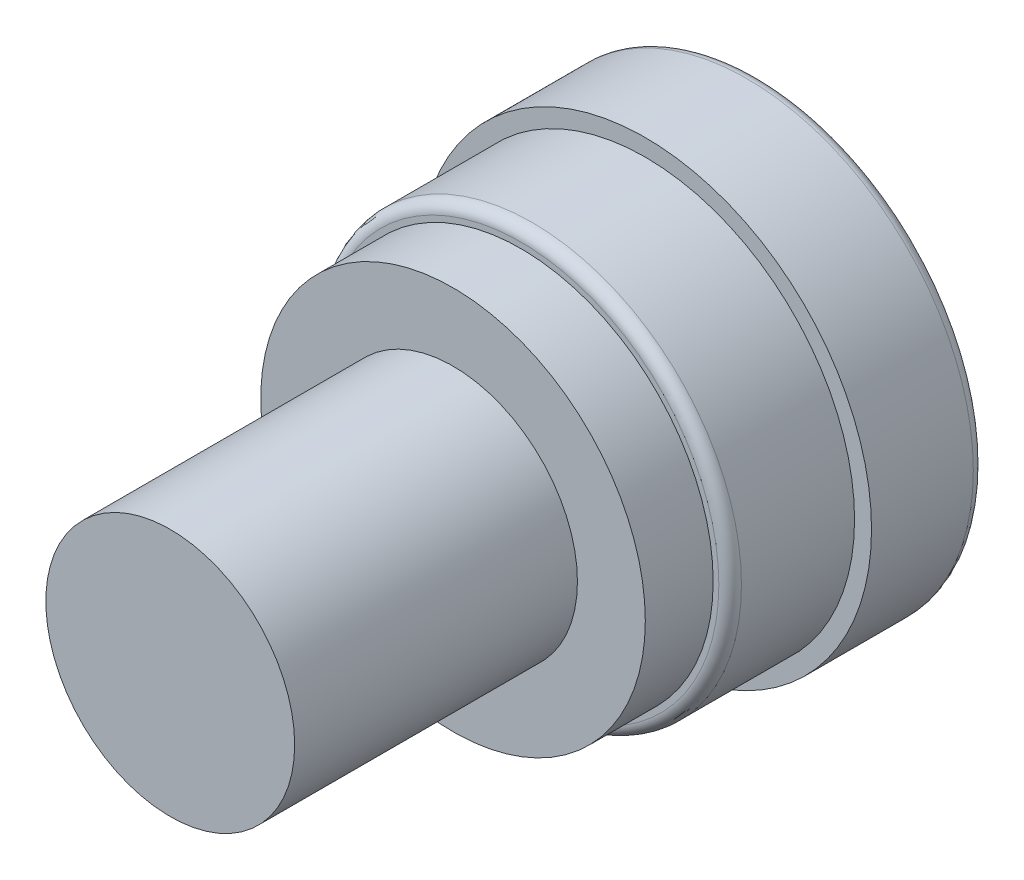
SolidWorks part; units mm, degrees
ref_plane "Front Plane" through (0, 0, 0) normal (0, 0, 1) x (1, 0, 0)
ref_plane "Top Plane" through (0, 0, 0) normal (0, 1, 0) x (1, 0, 0)
ref_plane "Right Plane" through (0, 0, 0) normal (1, 0, 0) x (0, 0, -1)
sketch "Sketch1" plane through (0, 0, 0) normal (0, 0, 1) x (1, 0, 0)
  circle A0 centre (0, 0) radius 20
  dimension "D1" = 40
extrude "Boss-Extrude1" add sketch "Sketch1" along normal blind 10
sketch "Sketch2" plane through (0, 0, 10) normal (0, 0, 1) x (1, 0, 0)
  circle A0 centre (0, 0) radius 18.5
  dimension "D1" = 37
extrude "Boss-Extrude2" add sketch "Sketch2" along normal blind 11
sketch "Sketch3" plane through (0, 0, 21) normal (0, 0, 1) x (1, 0, 0)
  circle A0 centre (0, 0) radius 17
  dimension "D1" = 34
extrude "Boss-Extrude3" add sketch "Sketch3" along normal blind 6
sketch "Sketch4" plane through (0, 0, 27) normal (0, 0, 1) x (1, 0, 0)
  circle A0 centre (0, 0) radius 11
  dimension "D1" = 22
extrude "Boss-Extrude4" add sketch "Sketch4" along normal blind 25
fillet "Fillet1" radius 1 2 edges at (18.5, 0, 21) (20, 0, 0)
